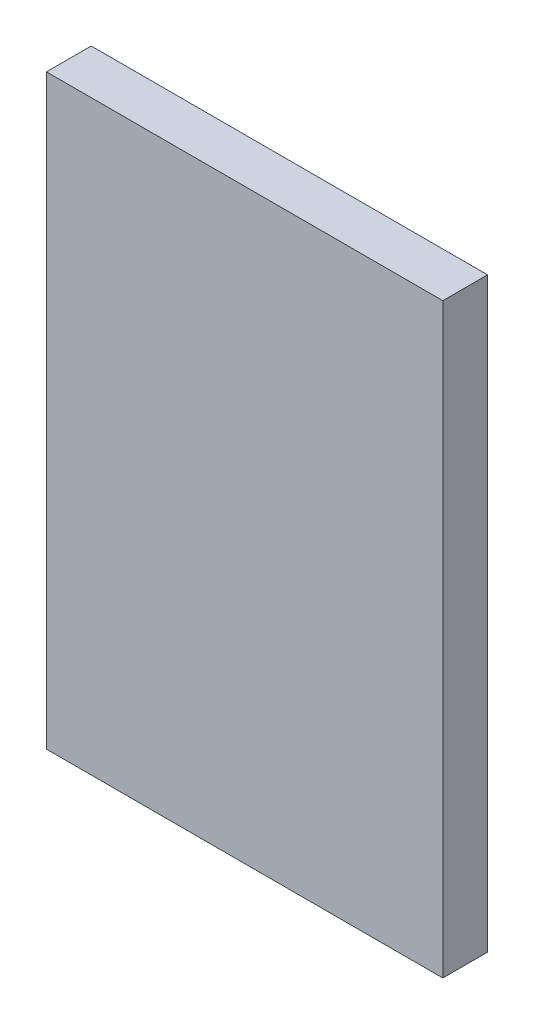
SolidWorks part; units mm, degrees
ref_plane "Alzado" through (0, 0, 0) normal (0, 0, 1) x (1, 0, 0)
ref_plane "Planta" through (0, 0, 0) normal (0, 1, 0) x (1, 0, 0)
ref_plane "Vista lateral" through (0, 0, 0) normal (1, 0, 0) x (0, 0, -1)
sketch "Croquis1" plane through (0, 0, 0) normal (0, 0, 1) x (1, 0, 0)
  line L1 (-225, 333) -> (225, 333)
  line L2 (-225, 333) -> (-225, -333)
  line L3 (-225, -333) -> (225, -333)
  line L4 (225, 333) -> (225, -333)
  line L5 (-225, 333) -> (225, -333) construction
  line L6 (-225, -333) -> (225, 333) construction
  point P0 (0, 0)
  dimension "D1" = 666
  dimension "D2" = 450
extrude "Saliente-Extruir1" add sketch "Croquis1" along normal blind 50.8
